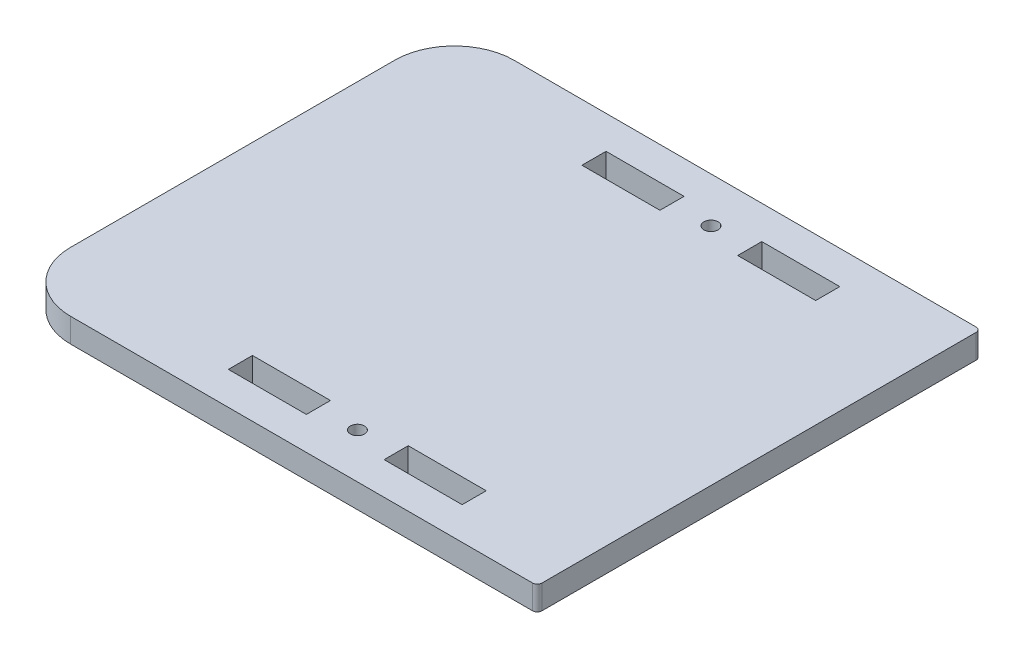
SolidWorks part; units mm, degrees
ref_plane "Front Plane" through (0, 0, 0) normal (0, 0, 1) x (1, 0, 0)
ref_plane "Top Plane" through (0, 0, 0) normal (0, 1, 0) x (1, 0, 0)
ref_plane "Right Plane" through (0, 0, 0) normal (1, 0, 0) x (0, 0, -1)
sketch "Sketch2" plane through (0, 0, 0) normal (0, 1, 0) x (1, 0, 0)
  line L0 (-210.3141, 2127.5217) -> (-210.3141, 2196.4817)
  line L1 (-98.3141, 2208.1817) -> (-98.3141, 2115.8217)
  line L4 (-99.3141, 2209.1817) -> (-197.6141, 2209.1817)
  line L5 (-197.6141, 2114.8217) -> (-99.3141, 2114.8217)
  line L6 (-137.8441, 2126.8915) -> (-121.2441, 2126.8915)
  line L7 (-137.8441, 2126.8915) -> (-137.8441, 2121.7615)
  line L8 (-171.0441, 2126.9517) -> (-154.4441, 2126.9517)
  line L9 (-137.8441, 2121.7615) -> (-121.2441, 2121.7615)
  line L10 (-121.2441, 2126.8915) -> (-121.2441, 2121.7615)
  line L11 (-171.0441, 2202.1809) -> (-154.4441, 2202.1809)
  line L12 (-171.0441, 2202.1809) -> (-171.0441, 2197.0509)
  line L13 (-171.0441, 2197.0509) -> (-154.4441, 2197.0509)
  line L14 (-154.4441, 2202.1809) -> (-154.4441, 2197.0509)
  line L15 (-137.8441, 2202.1207) -> (-121.2441, 2202.1207)
  line L16 (-137.8441, 2202.1207) -> (-137.8441, 2196.9907)
  line L17 (-137.8441, 2196.9907) -> (-121.2441, 2196.9907)
  line L18 (-121.2441, 2202.1207) -> (-121.2441, 2196.9907)
  line L20 (-110.4441, 18.564) -> (-105.3141, 18.564)
  line L30 (35.5186, 18.564) -> (40.6486, 18.564)
  line L31 (35.5186, 18.564) -> (35.5186, 1.964)
  line L32 (35.5186, 1.964) -> (40.6486, 1.964)
  line L33 (40.6486, 18.564) -> (40.6486, 1.964)
  line L34 (112.0498, -12.678) -> (117.1798, -12.678)
  line L35 (112.0498, -12.678) -> (112.0498, -29.278)
  line L36 (112.0498, -29.278) -> (117.1798, -29.278)
  line L37 (117.1798, -12.678) -> (117.1798, -29.278)
  line L38 (258.0126, -12.678) -> (263.1426, -12.678)
  line L39 (258.0126, -12.678) -> (258.0126, -29.278)
  line L40 (258.0126, -29.278) -> (263.1426, -29.278)
  line L41 (263.1426, -12.678) -> (263.1426, -29.278)
  line L45 (-110.4441, 18.564) -> (-110.4441, 1.964)
  line L46 (-110.4441, 1.964) -> (-105.3141, 1.964)
  line L48 (-105.3141, 18.564) -> (-105.3141, 1.964)
  line L137 (-171.0441, 2126.9517) -> (-171.0441, 2121.8217)
  line L138 (-171.0441, 2121.8217) -> (-154.4441, 2121.8217)
  line L139 (-154.4441, 2126.9517) -> (-154.4441, 2121.8217)
  circle A0 centre (-13.3165, 2181.0517) radius 1.4999
  circle A1 centre (-146.1441, 2199.6167) radius 1.5
  circle A2 centre (-146.1441, 2124.3867) radius 1.5
  circle A3 centre (38.2731, 2162.0017) radius 1.5
  arc A4 (-210.3141, 2196.4817) -> (-197.6141, 2209.1817) centre (-197.6141, 2196.4817) cw
  arc A5 (-197.6141, 2114.8217) -> (-210.3141, 2127.5217) centre (-197.6141, 2127.5217) cw
  arc A6 (-98.3141, 2208.1817) -> (-99.3141, 2209.1817) centre (-99.3141, 2208.1817) ccw
  circle A7 centre (-107.8791, -6.336) radius 1.5
  arc A8 (12.1907, 39.9983) -> (12.1904, 39.9976) centre (3163.8746, -1165.007) ccw
  arc A9 (1477.6026, 2566.4027) -> (1477.6026, 2566.4027) centre (3163.8746, 5489.0104) ccw
  circle A11 centre (102.673, 12.5121) radius 1.4999
  circle A12 centre (-47.3793, 2163.9832) radius 1.4999
  arc A13 (-98.3141, 2115.8217) -> (-99.3141, 2114.8217) centre (-99.3141, 2115.8217) cw
  circle A15 centre (-13.3165, 2181.0517) radius 1.25 construction
  circle A17 centre (68.6101, -4.5564) radius 1.4999
  point P7 (-210.3141, 2209.1817)
  point P32 (-210.3141, 2114.8217)
  point P35 (-98.3141, 2114.8217)
  point P37 (-210.3141, 2114.8217)
  point P38 (-98.3141, 2209.1817)
  point P65 (-98.3141, 2209.1817)
  point P68 (-98.3141, 2114.8217)
  dimension "D7" = 3
  dimension "D8" = 3
  dimension "D10" = 3
  dimension "D11" = 3
  dimension "D31" = 28.13
  dimension "D32" = 22.93
  dimension "D34" = 8.3
  dimension "D38" = 12.7
  dimension "D25" = 9.565
  dimension "D26" = 9.565
  dimension "D27" = 9.565
  dimension "D36" = 12.7
  dimension "D41" = 1
  dimension "D42" = 1
  dimension "D43" = 8.3
  dimension "D28" = 38.1
  dimension "D4" = 2
  dimension "D5" = 2
  dimension "D6" = 2
  dimension "D9" = 2
  dimension "D12" = 16.6
  dimension "D13" = 7
  dimension "D14" = 5.13
  dimension "D15" = 0
  dimension "D16" = 16.6
  dimension "D17" = 2
  dimension "D18" = 112
  dimension "D19" = 112
  dimension "D20" = 7
  dimension "D21" = 2
  dimension "D22" = 2
  dimension "D23" = 5.13
  dimension "D24" = 94.36
  dimension "D29" = 22.93
  dimension "D30" = 16.6
  dimension "D35" = 47.18
  dimension "D40" = 8.3
extrude "Boss-Extrude1" add sketch "Sketch2" along normal blind 5.13
hole_wizard "1/2 Clearance Hole1" positions "Sketch4" profile "Sketch3" hole size "1/2" standard "Ansi Inch"
sketch "Sketch4" plane through (0, 5.13, 0) normal (0, 1, 0) x (-1, 0, 0)
  circle A0 centre (-8.2735, -2159.4617) radius 5.7544 construction
  point P0 (-8.2735, -2159.4617)
sketch "Sketch3" plane through (8.2735, 5.13, -2159.4617) normal (1, 0, 0) x (0, 0, 1)
  line L0 (0, 0) -> (0, 5.13)
  line L1 (0, 5.13) -> (6.9456, 5.13)
  line L2 (6.9456, 5.13) -> (6.9456, 0)
  line L5 (6.9456, 0) -> (0, 0)
  line L11 (0, -6.35) -> (0, 107.95) construction
  dimension "Thru Hole Dia." = 13.8913
  dimension "Thru Hole Depth" = 5.13
equation "\"D35@Sketch2\" = \"D24@Sketch2\"/2"
equation "\"D31@Sketch2\" = (\"D24@Sketch2\"-\"D28@Sketch2\")/2"
